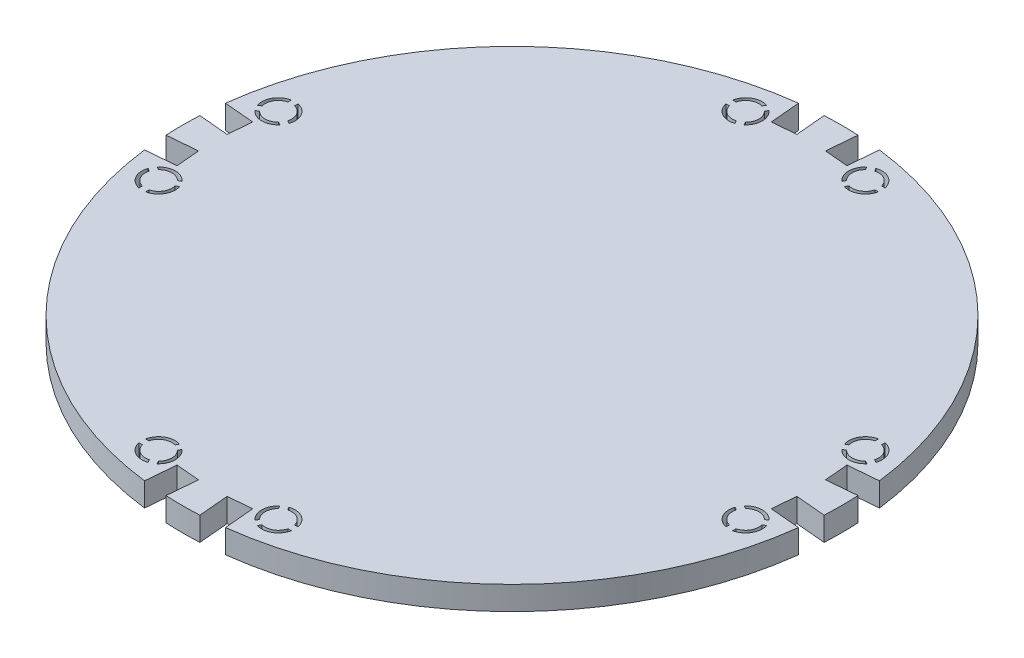
SolidWorks part; units mm, degrees
material "ABS PC"
ref_plane "Front Plane" through (0, 0, 0) normal (0, 0, 1) x (1, 0, 0)
ref_plane "Top Plane" through (0, 0, 0) normal (0, 1, 0) x (1, 0, 0)
ref_plane "Right Plane" through (0, 0, 0) normal (1, 0, 0) x (0, 0, -1)
sketch "Sketch2" plane through (0, 0, 0) normal (0, 1, 0) x (1, 0, 0)
  line L0 (-55, 0) -> (55, 0) construction
  line L1 (-57.0759, 2.7332) -> (-56.6834, 7.2195)
  line L2 (-56.6834, 7.2195) -> (-62.3893, 7.7187)
  line L3 (-62.6258, 5.479) -> (0, 0)
  line L4 (-57.0759, 2.7332) -> (-62.7818, 3.2324)
  line L5 (0, 0) -> (-5.479, 62.6258)
  line L6 (-7.2195, 56.6834) -> (-2.7332, 57.0759)
  line L7 (-7.2195, 56.6834) -> (-7.7187, 62.3893)
  line L8 (-2.7332, 57.0759) -> (-3.2324, 62.7818)
  line L9 (0, -55) -> (0, 55) construction
  circle A0 centre (0, 0) radius 62.865
  point P8 (-56.8797, 4.9763)
  point P14 (-4.9763, 56.8797)
  dimension "D4" = 125.73
  dimension "D1" = 5
  dimension "D2" = 4.5034
  dimension "D3" = 5.7277
  dimension "D5" = 5
extrude "Boss-Extrude1" add sketch "Sketch2" along normal mid plane 4.5034 contours A0
sketch "Sketch3" plane through (0, 2.2517, 0) normal (0, 1, 0) x (1, 0, 0)
  line L0 (-62.6258, 5.479) -> (0, 0) construction
  line L1 (0, 0) -> (-5.479, 62.6258) construction
  line L2 (-56.6834, 7.2195) -> (-62.3893, 7.7187) construction
  line L3 (-57.0759, 2.7332) -> (-56.6834, 7.2195) construction
  line L4 (-57.0759, 2.7332) -> (-62.7818, 3.2324) construction
  line L5 (-2.7332, 57.0759) -> (-3.2324, 62.7818) construction
  line L6 (-7.2195, 56.6834) -> (-2.7332, 57.0759) construction
  line L7 (-7.2195, 56.6834) -> (-7.7187, 62.3893) construction
  line L8 (-62.6258, 5.479) -> (0, 0)
  line L9 (0, 0) -> (-5.479, 62.6258)
  line L10 (-56.6834, 7.2195) -> (-62.3893, 7.7187)
  line L11 (-57.0759, 2.7332) -> (-56.6834, 7.2195)
  line L12 (-57.0759, 2.7332) -> (-62.7818, 3.2324)
  line L13 (-2.7332, 57.0759) -> (-3.2324, 62.7818)
  line L14 (-7.2195, 56.6834) -> (-2.7332, 57.0759)
  line L15 (-7.2195, 56.6834) -> (-7.7187, 62.3893)
  circle A1 centre (0, 0) radius 62.865
  circle A2 centre (0, 0) radius 62.865
  circle M2 centre (0, 0) radius 62.865
  dimension "D1" = 0
extrude "Cut-Extrude1" cut sketch "Sketch3" against normal blind 4.5034 contours L8 L11 L10 M2 | L12 L11 L8 M2 | L15 L14 L9 M2 | L9 L14 L13 M2
pattern_circular "CirPattern1" count 4 over 360 about axis through (0, 0, 0) along (0, 1, 0) of "Cut-Extrude1"
sketch "Sketch4" plane through (0, 2.2517, 0) normal (0, 1, 0) x (1, 0, 0)
  line L0 (0, 0) -> (-50.8, -87.9882)
  line L1 (0, 0) -> (50.8, -87.9882)
  line L2 (0, -55) -> (0, 55) construction
  circle A0 centre (0, 0) radius 101.6
  arc A1 (-19.05, -32.9956) -> (19.05, -32.9956) centre (0, 0) ccw
  line M1 (57.0759, 2.7332) -> (56.6834, 7.2195)
  line M2 (56.6834, 7.2195) -> (62.3893, 7.7187)
  arc M3 (62.3893, 7.7187) -> (7.7187, 62.3893) centre (0, 0) ccw
  line M4 (7.7187, 62.3893) -> (7.2195, 56.6834)
  line M5 (7.2195, 56.6834) -> (2.7332, 57.0759)
  line M6 (2.7332, 57.0759) -> (3.2324, 62.7818)
  arc M7 (3.2324, 62.7818) -> (-3.2324, 62.7818) centre (0, 0) ccw
  line M8 (-3.2324, 62.7818) -> (-2.7332, 57.0759)
  line M9 (-2.7332, 57.0759) -> (-7.2195, 56.6834)
  line M10 (-7.2195, 56.6834) -> (-7.7187, 62.3893)
  arc M11 (-7.7187, 62.3893) -> (-62.3893, 7.7187) centre (0, 0) ccw
  line M12 (-62.3893, 7.7187) -> (-56.6834, 7.2195)
  line M13 (-56.6834, 7.2195) -> (-57.0759, 2.7332)
  line M14 (-57.0759, 2.7332) -> (-62.7818, 3.2324)
  arc M15 (-62.7818, 3.2324) -> (-62.7818, -3.2324) centre (0, 0) ccw
  line M16 (-62.7818, -3.2324) -> (-57.0759, -2.7332)
  line M17 (-57.0759, -2.7332) -> (-56.6834, -7.2195)
  line M18 (-56.6834, -7.2195) -> (-62.3893, -7.7187)
  arc M19 (-62.3893, -7.7187) -> (-7.7187, -62.3893) centre (0, 0) ccw
  arc M27 (7.7187, -62.3893) -> (62.3893, -7.7187) centre (0, 0) ccw
  line M28 (62.3893, -7.7187) -> (56.6834, -7.2195)
  line M29 (56.6834, -7.2195) -> (57.0759, -2.7332)
  line M30 (57.0759, -2.7332) -> (62.7818, -3.2324)
  arc M31 (62.7818, -3.2324) -> (62.7818, 3.2324) centre (0, 0) ccw
  line M32 (62.7818, 3.2324) -> (57.0759, 2.7332)
  dimension "D4" = 38.1
  dimension "D1" = 30
  dimension "D2" = 60
  dimension "D3" = 101.6
extrude "Cut-Extrude2" [suppressed] cut sketch "Sketch4" against normal through all contours L1 A0 L0 M19 M18 M17 M16 M15 M14 M13 M12 M11 M10 M9 M8 M7 M6 M5 M4 M3 M2 M1 M32 M31 M30 M29 M28 M27 | L0 L1 M27 M28 M29 M30 M31 M32 M1 M2 M3 M4 M5 M6 M7 M8 M9 M10 M11 M12 M13 M14 M15 M16 M17 M18 M19 | L0 A1 L1
sketch "Sketch5" plane through (0, 2.2517, 0) normal (0, 1, 0) x (1, 0, 0)
  line L0 (-2.4769, 0) -> (2.4769, 0) construction
  line L1 (-58.745, -9.8425) -> (-55.9953, -11.43)
  line L2 (-59.0069, -10.4245) -> (-58.4427, -10.7503)
  line L3 (-58.3719, -9.3246) -> (-57.8077, -9.6504)
  line L4 (-55.9953, -11.43) -> (-53.2457, -9.8425)
  line L5 (-55.9953, -11.43) -> (-55.9953, -14.605)
  line L6 (-54.183, -9.6504) -> (-53.6188, -9.3246)
  line L7 (-53.548, -10.7503) -> (-52.9838, -10.4245)
  line L8 (-56.6303, -14.5409) -> (-56.6303, -13.8893)
  line L9 (-55.3603, -14.5409) -> (-55.3603, -13.8893)
  circle A0 centre (-55.9953, -11.43) radius 3.175
  arc A1 (-62.3893, -7.7187) -> (-7.7187, -62.3893) centre (0, 0) ccw construction
  circle A2 centre (-55.9953, -11.43) radius 2.54
  dimension "D2" = 57.15
  dimension "D3" = 6.35
  dimension "D12" = 0.635
  dimension "D1" = 11.43
  dimension "D4" = 1.27
  dimension "D5" = 0.635
  dimension "D6" = 120
  dimension "D7" = 120
  dimension "D8" = 1.27
  dimension "D9" = 0.635
  dimension "D10" = 1.27
  dimension "D11" = 0.635
extrude "Cut-Extrude3" cut sketch "Sketch5" against normal through all contours A2 L6 A0 L3 | A2 L2 A0 L8 | A2 L9 A0 L7
mirror "Mirror1" about plane through (0, 0, 0) normal (0, 0, 1) of "Cut-Extrude3"
pattern_circular "CirPattern2" count 4 over 360 about axis through (0, 0, 0) along (0, 1, 0) of "Cut-Extrude3", "Mirror1"
